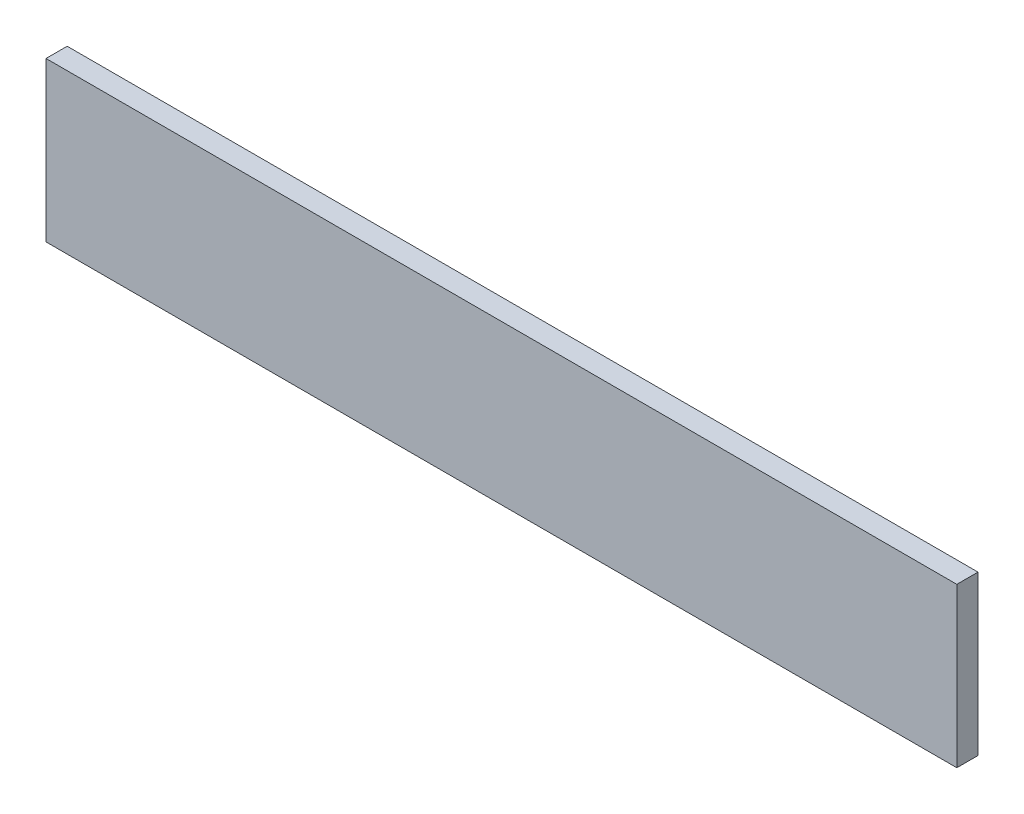
SolidWorks part; units mm, degrees
ref_plane "Alzado" through (0, 0, 0) normal (0, 0, 1) x (1, 0, 0)
ref_plane "Planta" through (0, 0, 0) normal (0, 1, 0) x (1, 0, 0)
ref_plane "Vista lateral" through (0, 0, 0) normal (1, 0, 0) x (0, 0, -1)
sketch "Croquis1" plane through (0, 0, 0) normal (0, 0, 1) x (1, 0, 0)
  line L1 (-613.9531, 236.8233) -> (246.0469, 236.8233)
  line L2 (-613.9531, 236.8233) -> (-613.9531, 86.8233)
  line L3 (-613.9531, 86.8233) -> (246.0469, 86.8233)
  line L4 (246.0469, 236.8233) -> (246.0469, 86.8233)
  dimension "D1" = 860
  dimension "D2" = 150
extrude "Saliente-Extruir1" add sketch "Croquis1" along normal blind 20
